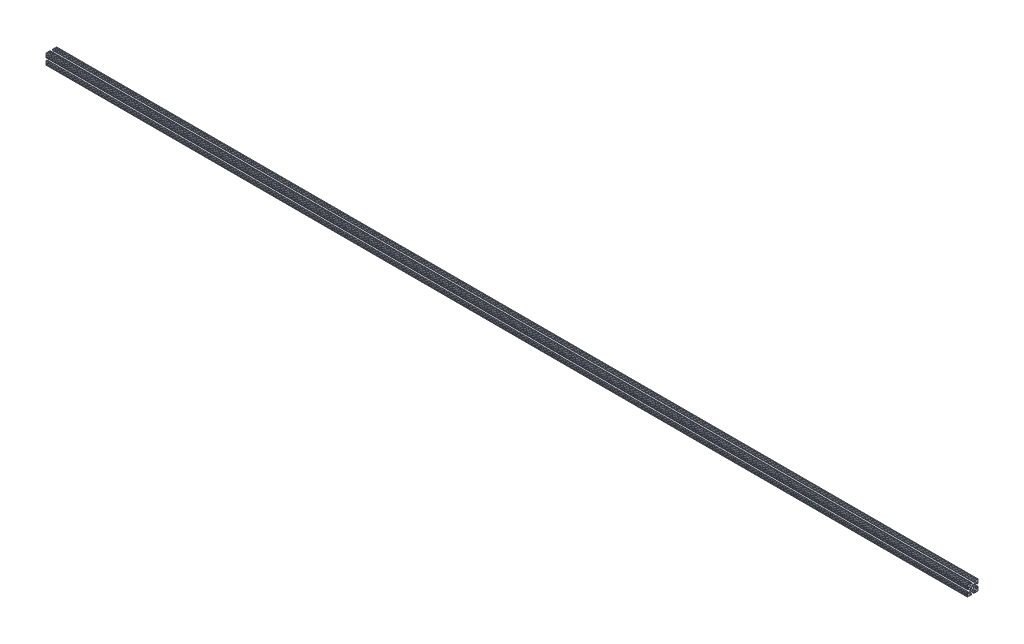
SolidWorks part; units mm, degrees
material "6063-T5"
ref_plane "Front Plane" through (0, 0, 0) normal (0, 0, 1) x (1, 0, 0)
ref_plane "Top Plane" through (0, 0, 0) normal (0, 1, 0) x (1, 0, 0)
ref_plane "Right Plane" through (0, 0, 0) normal (1, 0, 0) x (0, 0, -1)
sketch "Sketch1" plane through (0, 0, 0) normal (1, 0, 0) x (0, 0, -1)
  line L0 (-2.6035, 11.938) -> (-2.6035, 10.922)
  line L1 (-11.938, 12.7) -> (-9.9483, 12.7)
  line L2 (-12.7, 11.938) -> (-12.7, 9.9483)
  line L3 (-11.938, -12.7) -> (-9.9483, -12.7)
  line L4 (12.7, 11.938) -> (12.7, 9.9483)
  line L5 (-12.7, 12.7) -> (12.7, -12.7) construction
  line L6 (-12.7, -12.7) -> (12.7, 12.7) construction
  line L7 (-3.3655, 10.16) -> (-5.7804, 10.16)
  line L8 (-6.3192, 8.8592) -> (-2.8267, 5.3667)
  line L9 (-2.2879, 5.1435) -> (2.2879, 5.1435)
  line L10 (2.8267, 5.3667) -> (6.3192, 8.8592)
  line L11 (5.7804, 10.16) -> (3.3655, 10.16)
  line L12 (2.6035, 10.922) -> (2.6035, 11.938)
  line L13 (-8.6783, 12.7) -> (-6.5617, 12.7)
  line L14 (-5.2917, 12.7) -> (-3.3655, 12.7)
  line L15 (6.5618, 12.7) -> (8.6783, 12.7)
  line L16 (9.9483, 12.7) -> (11.938, 12.7)
  line L17 (3.3655, 12.7) -> (5.2918, 12.7)
  line L18 (10.16, 3.3655) -> (10.16, 5.7804)
  line L19 (8.8592, 6.3192) -> (5.3667, 2.8267)
  line L20 (10.16, -5.7804) -> (10.16, -3.3655)
  line L21 (10.922, -2.6035) -> (11.938, -2.6035)
  line L22 (5.3667, -2.8267) -> (8.8592, -6.3192)
  line L23 (5.1435, 2.2879) -> (5.1435, -2.2879)
  line L24 (11.938, 2.6035) -> (10.922, 2.6035)
  line L25 (3.3655, -10.16) -> (5.7804, -10.16)
  line L26 (6.3192, -8.8592) -> (2.8267, -5.3667)
  line L27 (-5.7804, -10.16) -> (-3.3655, -10.16)
  line L28 (-2.6035, -10.922) -> (-2.6035, -11.938)
  line L29 (-2.8267, -5.3667) -> (-6.3192, -8.8592)
  line L30 (2.2879, -5.1435) -> (-2.2879, -5.1435)
  line L31 (2.6035, -11.938) -> (2.6035, -10.922)
  line L32 (-10.16, -3.3655) -> (-10.16, -5.7804)
  line L33 (-8.8592, -6.3192) -> (-5.3667, -2.8267)
  line L34 (-10.16, 5.7804) -> (-10.16, 3.3655)
  line L35 (-10.922, 2.6035) -> (-11.938, 2.6035)
  line L36 (-5.3667, 2.8267) -> (-8.8592, 6.3192)
  line L37 (-5.1435, -2.2879) -> (-5.1435, 2.2879)
  line L38 (-11.938, -2.6035) -> (-10.922, -2.6035)
  line L39 (-12.7, 8.6783) -> (-12.7, 6.5618)
  line L40 (-12.7, 5.2918) -> (-12.7, 3.3655)
  line L41 (-12.7, -3.3655) -> (-12.7, -5.2917)
  line L42 (-12.7, -6.5617) -> (-12.7, -8.6783)
  line L43 (-12.7, -9.9483) -> (-12.7, -11.938)
  line L44 (-8.6783, -12.7) -> (-6.5618, -12.7)
  line L45 (-5.2918, -12.7) -> (-3.3655, -12.7)
  line L46 (3.3655, -12.7) -> (5.2917, -12.7)
  line L47 (6.5617, -12.7) -> (8.6783, -12.7)
  line L48 (9.9483, -12.7) -> (11.938, -12.7)
  line L49 (12.7, -9.9483) -> (12.7, -11.938)
  line L50 (12.7, -6.5618) -> (12.7, -8.6783)
  line L51 (12.7, -3.3655) -> (12.7, -5.2918)
  line L52 (12.7, 5.2917) -> (12.7, 3.3655)
  line L53 (12.7, 8.6783) -> (12.7, 6.5617)
  arc A1 (5.2918, 12.7) -> (6.5618, 12.7) centre (5.9268, 12.7) ccw
  arc A2 (8.6783, 12.7) -> (9.9483, 12.7) centre (9.3133, 12.7) ccw
  arc A3 (-6.5617, 12.7) -> (-5.2917, 12.7) centre (-5.9267, 12.7) ccw
  arc A4 (-9.9483, 12.7) -> (-8.6783, 12.7) centre (-9.3133, 12.7) ccw
  arc A5 (12.7, 9.9483) -> (12.7, 8.6783) centre (12.7, 9.3133) ccw
  arc A6 (12.7, 6.5617) -> (12.7, 5.2917) centre (12.7, 5.9267) ccw
  arc A7 (12.7, -5.2918) -> (12.7, -6.5618) centre (12.7, -5.9268) ccw
  arc A8 (12.7, -8.6783) -> (12.7, -9.9483) centre (12.7, -9.3133) ccw
  arc A9 (9.9483, -12.7) -> (8.6783, -12.7) centre (9.3133, -12.7) ccw
  arc A10 (6.5617, -12.7) -> (5.2917, -12.7) centre (5.9267, -12.7) ccw
  arc A11 (-5.2918, -12.7) -> (-6.5618, -12.7) centre (-5.9268, -12.7) ccw
  arc A12 (-8.6783, -12.7) -> (-9.9483, -12.7) centre (-9.3133, -12.7) ccw
  arc A13 (-12.7, -9.9483) -> (-12.7, -8.6783) centre (-12.7, -9.3133) ccw
  arc A14 (-12.7, -6.5617) -> (-12.7, -5.2917) centre (-12.7, -5.9267) ccw
  arc A15 (-12.7, 5.2918) -> (-12.7, 6.5618) centre (-12.7, 5.9268) ccw
  arc A16 (-12.7, 8.6783) -> (-12.7, 9.9483) centre (-12.7, 9.3133) ccw
  arc A17 (-11.938, -2.6035) -> (-12.7, -3.3655) centre (-11.938, -3.3655) ccw
  arc A18 (-10.922, -2.6035) -> (-10.16, -3.3655) centre (-10.922, -3.3655) cw
  arc A19 (-10.16, -5.7804) -> (-8.8592, -6.3192) centre (-9.398, -5.7804) ccw
  arc A20 (-6.3192, -8.8592) -> (-5.7804, -10.16) centre (-5.7804, -9.398) ccw
  arc A21 (-3.3655, -10.16) -> (-2.6035, -10.922) centre (-3.3655, -10.922) cw
  arc A22 (-3.3655, -12.7) -> (-2.6035, -11.938) centre (-3.3655, -11.938) ccw
  arc A23 (2.6035, -10.922) -> (3.3655, -10.16) centre (3.3655, -10.922) cw
  arc A24 (2.6035, -11.938) -> (3.3655, -12.7) centre (3.3655, -11.938) ccw
  arc A25 (5.7804, -10.16) -> (6.3192, -8.8592) centre (5.7804, -9.398) ccw
  arc A26 (8.8592, -6.3192) -> (10.16, -5.7804) centre (9.398, -5.7804) ccw
  arc A27 (11.938, -2.6035) -> (12.7, -3.3655) centre (11.938, -3.3655) cw
  arc A28 (10.922, -2.6035) -> (10.16, -3.3655) centre (10.922, -3.3655) ccw
  arc A29 (11.938, 2.6035) -> (12.7, 3.3655) centre (11.938, 3.3655) ccw
  arc A30 (10.922, 2.6035) -> (10.16, 3.3655) centre (10.922, 3.3655) cw
  arc A31 (10.16, 5.7804) -> (8.8592, 6.3192) centre (9.398, 5.7804) ccw
  arc A32 (6.3192, 8.8592) -> (5.7804, 10.16) centre (5.7804, 9.398) ccw
  arc A33 (2.6035, 11.938) -> (3.3655, 12.7) centre (3.3655, 11.938) cw
  arc A34 (3.3655, 10.16) -> (2.6035, 10.922) centre (3.3655, 10.922) cw
  arc A35 (-2.6035, 11.938) -> (-3.3655, 12.7) centre (-3.3655, 11.938) ccw
  arc A36 (-2.6035, 10.922) -> (-3.3655, 10.16) centre (-3.3655, 10.922) cw
  arc A37 (-5.7804, 10.16) -> (-6.3192, 8.8592) centre (-5.7804, 9.398) ccw
  arc A38 (-8.8592, 6.3192) -> (-10.16, 5.7804) centre (-9.398, 5.7804) ccw
  arc A39 (-10.16, 3.3655) -> (-10.922, 2.6035) centre (-10.922, 3.3655) cw
  arc A40 (-11.938, 2.6035) -> (-12.7, 3.3655) centre (-11.938, 3.3655) cw
  arc A41 (11.938, 12.7) -> (12.7, 11.938) centre (11.938, 11.938) cw
  arc A42 (12.7, -11.938) -> (11.938, -12.7) centre (11.938, -11.938) cw
  arc A43 (-11.938, -12.7) -> (-12.7, -11.938) centre (-11.938, -11.938) cw
  arc A44 (-11.938, 12.7) -> (-12.7, 11.938) centre (-11.938, 11.938) ccw
  arc A45 (-2.2879, -5.1435) -> (-2.8267, -5.3667) centre (-2.2879, -5.9055) ccw
  arc A46 (2.2879, -5.1435) -> (2.8267, -5.3667) centre (2.2879, -5.9055) cw
  arc A47 (5.1435, -2.2879) -> (5.3667, -2.8267) centre (5.9055, -2.2879) ccw
  arc A48 (5.3667, 2.8267) -> (5.1435, 2.2879) centre (5.9055, 2.2879) ccw
  arc A49 (-2.8267, 5.3667) -> (-2.2879, 5.1435) centre (-2.2879, 5.9055) ccw
  arc A50 (2.2879, 5.1435) -> (2.8267, 5.3667) centre (2.2879, 5.9055) ccw
  arc A51 (-5.1435, 2.2879) -> (-5.3667, 2.8267) centre (-5.9055, 2.2879) ccw
  arc A52 (-5.1435, -2.2879) -> (-5.3667, -2.8267) centre (-5.9055, -2.2879) cw
  point P0 (0, 0)
  point P17 (0, 5.1435)
  point P92 (0, 0)
  point P124 (2.6035, 12.7)
  point P127 (2.6035, 10.16)
  point P130 (-2.6035, 12.7)
  point P133 (-2.6035, 10.16)
  point P164 (-2.6035, 5.1435)
  point P167 (2.6035, 5.1435)
  dimension "D7" = 1.27
  dimension "D8" = 1.27
  dimension "D9" = 1.27
  dimension "D10" = 1.27
  dimension "D2" = 0.762
  dimension "D16" = 0.762
  dimension "D1" = 25.4
  dimension "D4" = 2.54
  dimension "D5" = 5.207
  dimension "D11" = 3.3867
  dimension "D12" = 3.3866
  dimension "D13" = 3.3867
  dimension "D14" = 3.3867
  dimension "D15" = 4
extrude "Boss-Extrude1" add sketch "Sketch1" along normal blind 2184.4 contours L40 A40 L35 A39 L34 A38 L36 A51 L37 A52 L33 A19 L32 A18 L38 A17 L41 A14 L42 A13 L43 A43 L3 A12 L44 A11 L45 A22 L28 A21 L27 A20 L29 A45 L30 A46 L26 A25 L25 A23 L31 A24 L46 A10 L47 A9 L48 A42 L49 A8 L50 A7 L51 A27 L21 A28 L20 A26 L22 A47 L23 A48 L19 A31 L18 A30 L24 A29 L52 A6 L53 A5 L4 A41 L16 A2 L15 A1 L17 A33 L12 A34 L11 A32 L10 A50 L9 A49 L8 A37 L7 A36 L0 A35 L14 A3 L13 A4 L1 A44 L2 A16 L39 A15
sketch "Sketch2" plane through (0, 0, 0) normal (-1, 0, 0) x (0, 0, 1)
  circle A0 centre (0, 0) radius 2.6035
  dimension "D1" = 5.207
extrude "Cut-Extrude1" cut sketch "Sketch2" against normal up to surface (2184.4 mm away) up to face at (2184.4, 0, 0)
